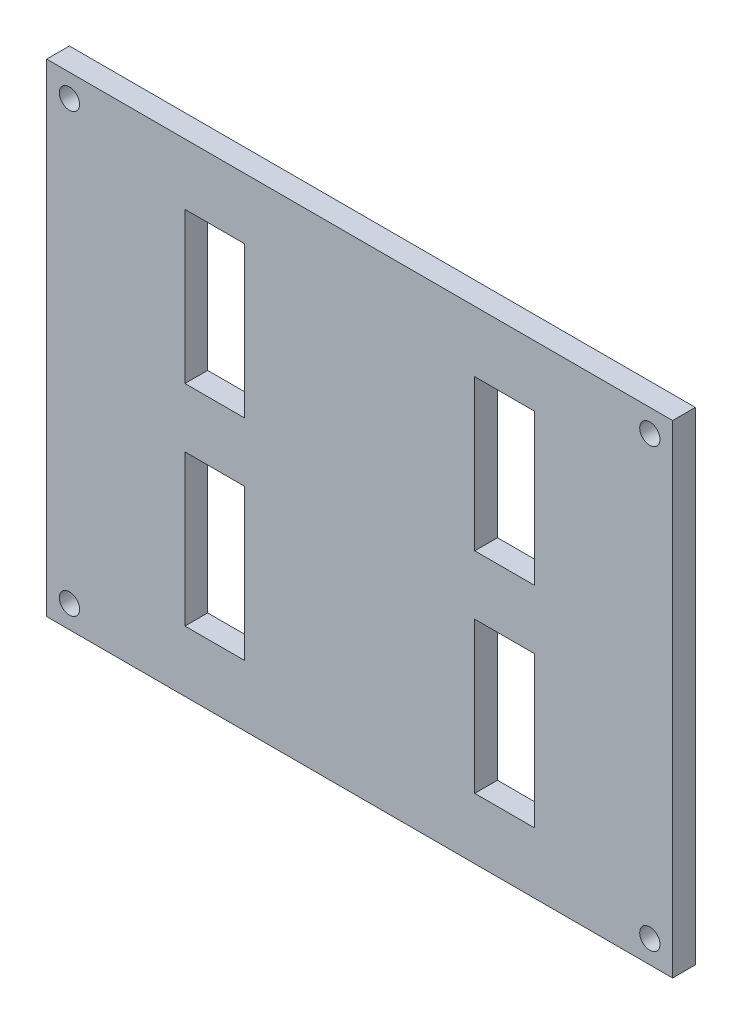
SolidWorks part; units mm, degrees
material "Maple"
ref_plane "Front Plane" through (0, 0, 0) normal (0, 0, 1) x (1, 0, 0)
ref_plane "Top Plane" through (0, 0, 0) normal (0, 1, 0) x (1, 0, 0)
ref_plane "Right Plane" through (0, 0, 0) normal (1, 0, 0) x (0, 0, -1)
sketch "Sketch1" plane through (0, 0, 0) normal (0, 0, 1) x (1, 0, 0)
  line L1 (-50, 40) -> (50, 40)
  line L2 (-50, 40) -> (-50, -40)
  line L3 (-50, -40) -> (50, -40)
  line L4 (50, 40) -> (50, -40)
  line L5 (-50, 40) -> (50, -40) construction
  line L6 (-50, -40) -> (50, 40) construction
  point P0 (0, 0)
  dimension "D1" = 100
  dimension "D2" = 80
extrude "Boss-Extrude1" add sketch "Sketch1" along normal blind 3.175
sketch "Sketch2" plane through (0, 0, 3.175) normal (0, 0, 1) x (1, 0, 0)
  line L0 (-35.3, 25.3) -> (-35.3, -25.3) construction
  line L1 (-37.3, 27.3) -> (37.3, 27.3) construction
  line L2 (-37.3, 27.3) -> (-37.3, -27.3) construction
  line L3 (-37.3, -27.3) -> (37.3, -27.3) construction
  line L4 (37.3, 27.3) -> (37.3, -27.3) construction
  line L5 (-37.3, 27.3) -> (37.3, -27.3) construction
  line L6 (-37.3, -27.3) -> (37.3, 27.3) construction
  line L7 (-35.3, -25.3) -> (35.3, -25.3) construction
  line L8 (35.3, 25.3) -> (35.3, -25.3) construction
  line L9 (-35.3, 25.3) -> (35.3, 25.3) construction
  line L10 (35.3, 0) -> (16, 0) construction
  line L11 (16, 0) -> (16, 25.3) construction
  line L12 (16, -4.05) -> (24.5, -4.05)
  line L13 (16, 25.3) -> (24.5, 25.3)
  line L14 (16, 25.3) -> (16, 4.05)
  line L15 (16, 4.05) -> (24.5, 4.05)
  line L16 (24.5, 25.3) -> (24.5, 4.05)
  line L17 (24.5, -25.3) -> (24.5, -4.05)
  line L18 (16, -25.3) -> (24.5, -25.3)
  line L19 (16, -25.3) -> (16, -4.05)
  line L20 (0, 0) -> (0, -8.4087) construction
  line L21 (-16, -25.3) -> (-16, -4.05)
  line L22 (-16, -25.3) -> (-24.5, -25.3)
  line L23 (-24.5, -25.3) -> (-24.5, -4.05)
  line L24 (-16, -4.05) -> (-24.5, -4.05)
  line L25 (-16, 4.05) -> (-24.5, 4.05)
  line L26 (-24.5, 25.3) -> (-24.5, 4.05)
  line L27 (-16, 25.3) -> (-24.5, 25.3)
  line L28 (-16, 25.3) -> (-16, 4.05)
  line L29 (-16.085, 4.135) -> (-24.415, 4.135)
  line L30 (-24.415, 25.215) -> (-24.415, 4.135)
  line L31 (-16.085, 25.215) -> (-24.415, 25.215)
  line L32 (-16.085, 25.215) -> (-16.085, 4.135)
  line L33 (16.085, 25.215) -> (16.085, 4.135)
  line L34 (16.085, 4.135) -> (24.415, 4.135)
  line L35 (24.415, 25.215) -> (24.415, 4.135)
  line L36 (16.085, 25.215) -> (24.415, 25.215)
  line L37 (-16.085, -25.215) -> (-16.085, -4.135)
  line L38 (-16.085, -4.135) -> (-24.415, -4.135)
  line L39 (-24.415, -25.215) -> (-24.415, -4.135)
  line L40 (-16.085, -25.215) -> (-24.415, -25.215)
  line L41 (16.085, -4.135) -> (24.415, -4.135)
  line L42 (24.415, -25.215) -> (24.415, -4.135)
  line L43 (16.085, -25.215) -> (24.415, -25.215)
  line L44 (16.085, -25.215) -> (16.085, -4.135)
  point P0 (0, 0)
  point P12 (29.05, 0)
  dimension "D1" = 74.6
  dimension "D2" = 54.6
  dimension "D4" = 19.3
  dimension "D5" = 6.25
  dimension "D6" = 8.5
  dimension "D7" = 21.25
  dimension "D3" = 2
  dimension "D8" = 0.085
  dimension "D9" = 0.085
  dimension "D10" = 0.085
  dimension "D11" = 0.085
sketch "Sketch3" plane through (0, 0, 3.175) normal (0, 0, 1) x (1, 0, 0)
  line L0 (-50.085, 40.085) -> (50.085, 40.085)
  line L1 (-43.735, 33.735) -> (43.735, 33.735)
  line L2 (-43.735, 33.735) -> (-43.735, -33.735)
  line L3 (-43.735, -33.735) -> (43.735, -33.735)
  line L4 (43.735, 33.735) -> (43.735, -33.735)
  line L5 (-43.735, 33.735) -> (43.735, -33.735) construction
  line L6 (-43.735, -33.735) -> (43.735, 33.735) construction
  line L7 (50.085, 40.085) -> (50.085, -40.085)
  line L8 (-50.085, -40.085) -> (50.085, -40.085)
  line L9 (-50.085, 40.085) -> (-50.085, -40.085)
  point P0 (0, 0)
  dimension "D1" = 87.47
  dimension "D2" = 67.47
  dimension "D3" = 6.35
extrude "Cut-Extrude2" cut sketch "Sketch3" against normal blind 10
sketch "Sketch4" plane through (0, 0, 3.175) normal (0, 0, 1) x (1, 0, 0)
  line L0 (-43.735, 33.735) -> (-40.553, 30.553) construction
  line L1 (43.735, 33.735) -> (-43.735, 33.735) construction
  line L2 (0, 0) -> (0, -8.8736) construction
  line L3 (0, 0) -> (-13.9667, 0) construction
  circle A0 centre (-40.553, 30.553) radius 1.415
  circle A1 centre (40.553, 30.553) radius 1.415
  circle A2 centre (40.553, -30.553) radius 1.415
  circle A3 centre (-40.553, -30.553) radius 1.415
  dimension "D3" = 2.83
  dimension "D1" = 45
  dimension "D2" = 4.5
extrude "Cut-Extrude3" cut sketch "Sketch4" against normal blind 10
extrude "Cut-Extrude4" cut sketch "Sketch2" against normal blind 10 contours L29 L30 L31 L32 | L37 L38 L39 L40 | L33 L34 L35 L36 | L41 L42 L43 L44
equation "\"length\"= 100mm"
equation "\"width\"= 80mm"
equation "\"depth\"= 6.35mm"
equation "\"D1@Sketch2\"=\"length\"- 4*\"depth\""
equation "\"D2@Sketch2\"=\"width\"- 4*\"depth\" "
equation "\"kerf\"= 0.17 / 2"
equation "\"D2@Sketch3\"= 67.30mm + 2*\"kerf\""
equation "\"D1@Sketch3\"= 87.30mm + 2*\"kerf\""
equation "\"D3@Sketch4\"= 3.00mm - 2*\"kerf\""
equation "\"D6@Sketch2\"=8.50mm"
equation "\"D7@Sketch2\"=21.25mm"
equation "\"D3@Sketch2\"=2.00mm"
